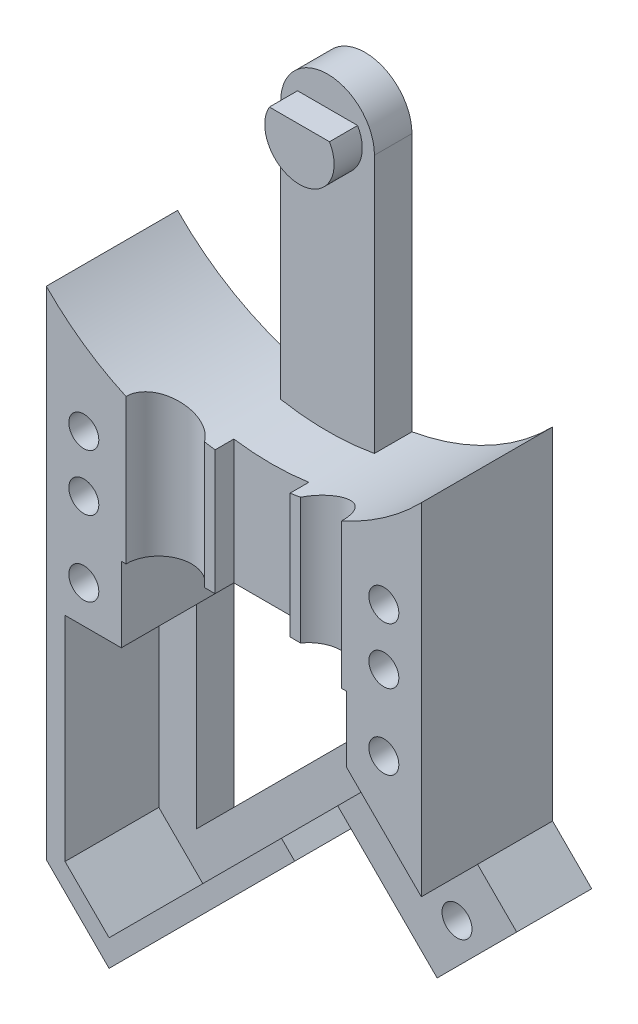
SolidWorks part; units mm, degrees
ref_plane "Front" through (0, 0, 0) normal (0, 0, 1) x (1, 0, 0)
ref_plane "Top" through (0, 0, 0) normal (0, 1, 0) x (1, 0, 0)
ref_plane "Right" through (0, 0, 0) normal (1, 0, 0) x (0, 0, -1)
sketch "Sketch1" plane through (0, 0, 0) normal (0, 0, 1) x (1, 0, 0)
  line L2 (20, -19) -> (17.8431, -16.8431) construction
  line L3 (17.8431, -25.3284) -> (29.1568, -36.6421) construction
  line L4 (29.1568, -36.6421) -> (33.3995, -32.3995) construction
  line L5 (33.3995, -32.3995) -> (22.0857, -21.0857) construction
  line L6 (13.2469, -20.7322) -> (3.3474, -30.6317)
  line L7 (3.3474, -30.6317) -> (0, -27.2843)
  line L8 (13.2469, -20.7322) -> (17.8431, -25.3284)
  line L9 (20, -19) -> (20, -0.798)
  line L10 (1, -15.5) -> (1, -26.8701)
  line L11 (17.8431, -25.3284) -> (22.0857, -21.0857)
  line L12 (22.0857, -21.0857) -> (20, -19)
  line L13 (4, -11.5) -> (4, -15.5)
  line L14 (10, -5) -> (10, 9) construction
  line L15 (4, -11.5) -> (16, -11.5)
  line L16 (1, -26.8701) -> (3.3474, -29.2175)
  line L17 (0, -27.2843) -> (0, -0.798)
  line L18 (16, -11.5) -> (16, -16.5649)
  line L19 (4, -15.5) -> (1, -15.5)
  line L20 (16, -16.5649) -> (3.3474, -29.2175)
  arc A0 (0, -0.798) -> (20, -0.798) centre (10, 9) ccw
extrude "Boss-Extrude1" add sketch "Sketch1" along normal blind 7
sketch "Sketch6" plane through (0, 0, 0) normal (0, 0, 1) x (1, 0, 0)
  line L0 (1, -11.5) -> (3, -11.5)
  line L1 (19, -11.5) -> (19, -18)
  line L2 (1, -11.5) -> (1, -26.8701)
  line L3 (1, -26.8701) -> (3.3474, -29.2175)
  line L4 (19, -18) -> (17.8431, -16.8431)
  line L5 (17.8431, -16.8431) -> (14.3076, -20.3786)
  line L6 (3.3474, -29.2175) -> (13.2469, -19.318)
  line L7 (13.2469, -19.318) -> (14.3076, -20.3786)
  line L8 (3, -11.5) -> (3, -26.8701)
  line L9 (19, -11.5) -> (17, -11.5)
  line L10 (3, -26.8701) -> (17, -12.8701)
  line L11 (17, -12.8701) -> (17, -11.5)
extrude "Boss-Extrude2" add sketch "Sketch6" along normal blind 2
sketch "Sketch8" plane through (0, 0, 0) normal (0, 0, 1) x (1, 0, 0)
  line L0 (10, -5) -> (10, -11.5) construction
  line L1 (10, -11.5) -> (12.5, -11.5)
  line L2 (12.5, -11.5) -> (12.5, 9)
  line L3 (10, -11.5) -> (7.5, -11.5)
  line L4 (7.5, -11.5) -> (7.5, 9)
  arc A0 (12.5, 9) -> (7.5, 9) centre (10, 9) ccw
extrude "Boss-Extrude3" add sketch "Sketch8" along normal blind 2
sketch "Sketch9" plane through (0, 0, 0) normal (0, 0, 1) x (1, 0, 0)
  line L0 (10, 9) -> (10, 9.925) construction
  line L1 (8.3979, 9.925) -> (11.6021, 9.925)
  arc A1 (8.3979, 9.925) -> (11.6021, 9.925) centre (10, 9) ccw
extrude "Boss-Extrude4" add sketch "Sketch9" along normal blind 1.5 from offset 2
sketch "Sketch3" plane through (0, 0, 0) normal (0, 1, 0) x (1, 0, 0)
  line L0 (6, -6) -> (8, -6)
  line L1 (8, -6) -> (8, -5)
  line L2 (8, -5) -> (12, -5)
  line L3 (12, -5) -> (12, -6)
  line L4 (12, -6) -> (14, -6)
  line L20 (10, -7) -> (14, -7) construction
  line L23 (10, -7) -> (6, -7) construction
  line L24 (14, -7) -> (14, -6)
  line L34 (6, -6) -> (6, -7)
  line L35 (6, -7) -> (14, -7)
  circle A2 centre (6, -7) radius 1.75
  circle A3 centre (14, -7) radius 1.75
extrude "Wire and Tube Canals" cut sketch "Sketch3" against normal blind 8.5 from offset 3
sketch "Sketch5" plane through (0, 0, 0) normal (0, 0, 1) x (1, 0, 0)
  line L0 (10, -5) -> (10, -6.5) construction
  line L1 (10, -13.5) -> (18, -13.5) construction
  line L2 (10, -6.5) -> (18, -6.5) construction
  line L3 (10, -6.5) -> (10, -9.5) construction
  line L4 (10, -9.5) -> (18, -9.5) construction
  line L5 (10, -6.5) -> (2, -6.5) construction
  line L6 (19.9644, -23.2071) -> (18.9038, -22.1464) construction
  line L7 (10, -9.5) -> (2, -9.5) construction
  line L8 (17.8431, -25.3284) -> (22.0857, -21.0857) construction
  line L9 (18.9038, -22.1464) -> (16.7824, -20.0251) construction
  line L10 (2, -13.5) -> (10, -13.5) construction
  line L11 (10, -13.5) -> (10, -9.5) construction
  circle A0 centre (2, -6.5) radius 0.8
  circle A1 centre (2, -9.5) radius 0.8
  circle A2 centre (18, -9.5) radius 0.8
  circle A3 centre (18, -6.5) radius 0.8
  circle A4 centre (18.9038, -22.1464) radius 0.8
  circle A5 centre (16.7824, -20.0251) radius 0.8
  circle A6 centre (2, -13.5) radius 0.8
  circle A7 centre (18, -13.5) radius 0.8
extrude "Screw Holes" cut sketch "Sketch5" along normal through all
sketch "Sketch10" plane through (0, 0, 0) normal (0, 0, 1) x (1, 0, 0)
  line L0 (17.8431, -25.3284) -> (22.0857, -21.0857)
  line L1 (22.0857, -21.0857) -> (15.7218, -14.7218)
  line L2 (15.7218, -14.7218) -> (11.4791, -18.9644)
  line L4 (11.4791, -18.9644) -> (17.8431, -25.3284)
extrude "Cut-Extrude1" cut sketch "Sketch10" along normal blind 3 from offset 4
